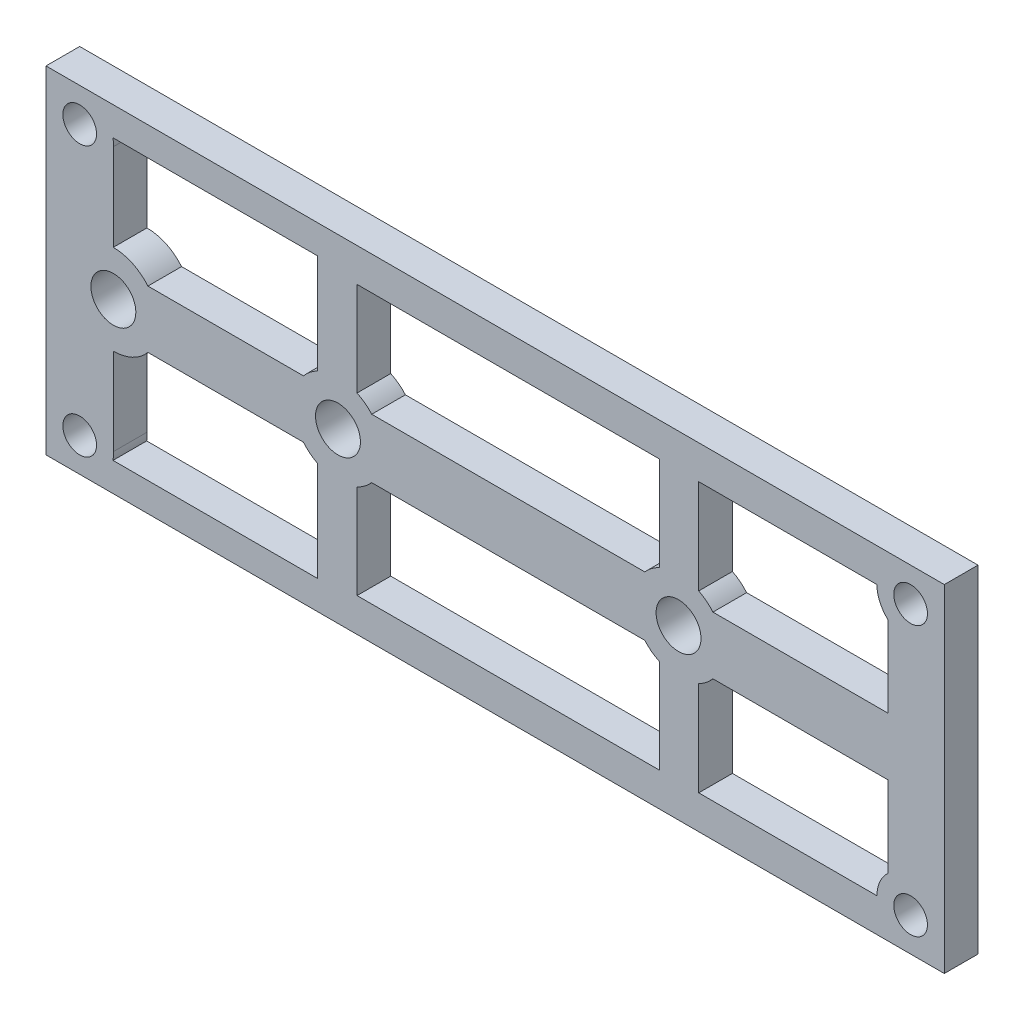
SolidWorks part; units mm, degrees
ref_plane "Front Plane" through (0, 0, 0) normal (0, 0, 1) x (1, 0, 0)
ref_plane "Top Plane" through (0, 0, 0) normal (0, 1, 0) x (1, 0, 0)
ref_plane "Right Plane" through (0, 0, 0) normal (1, 0, 0) x (0, 0, -1)
sketch "Sketch1" plane through (0, 0, 0) normal (0, 0, 1) x (1, 0, 0)
  line L1 (40, -15) -> (-40, -15)
  line L2 (40, -15) -> (40, 15)
  line L3 (40, 15) -> (-40, 15)
  line L4 (-40, -15) -> (-40, 15)
  line L5 (40, -15) -> (-40, 15) construction
  line L6 (40, 15) -> (-40, -15) construction
  point P0 (0, 0)
  dimension "D1" = 80
  dimension "D2" = 30
extrude "Boss-Extrude1" add sketch "Sketch1" along normal blind 3
sketch "Sketch2" plane through (0, 0, 3) normal (0, 0, 1) x (1, 0, 0)
  line L0 (-40, 15) -> (-40, -15) construction
  line L2 (40, 15) -> (-40, 15) construction
  line L3 (-34.0325, 12.4402) -> (-15.8, 12.4402)
  line L4 (40, -15) -> (40, 15) construction
  line L5 (-34.0097, 11.7592) -> (-34.0097, 4)
  line L6 (0, -1.65) -> (0, 1.65) construction
  line L7 (1.65, 0) -> (-1.65, 0) construction
  line L8 (-30.9254, 2.5586) -> (-17.0746, 2.5586)
  line L9 (-15.8, 12.4402) -> (-15.8, 3.5721)
  line L10 (13.3233, 2.6382) -> (-10.9933, 2.6382)
  line L11 (14.63, 3.6208) -> (14.63, 12)
  line L12 (14.63, 12) -> (-12.3, 12)
  line L13 (-12.3, 3.6208) -> (-12.3, 12)
  line L14 (35, 2.5718) -> (19.3936, 2.5718)
  line L15 (35, 2.5718) -> (35, 9.7639)
  line L16 (34, 12) -> (18.13, 12)
  line L17 (18.13, 3.5721) -> (18.13, 12)
  circle A0 centre (37, 12) radius 1.5
  circle A1 centre (-37, 12) radius 1.5
  circle A2 centre (37, -12) radius 1.5
  circle A3 centre (-37, -12) radius 1.5
  circle A4 centre (-14, 0) radius 2
  circle A5 centre (-34, 0) radius 2
  circle A6 centre (16.33, 0) radius 2
  arc A7 (-10.9933, 2.6382) -> (-12.3, 3.6208) centre (-14, 0) ccw
  arc A8 (14.63, 3.6208) -> (13.3233, 2.6382) centre (16.33, 0) ccw
  arc A9 (-30.9254, 2.5586) -> (-34.0097, 4) centre (-34, 0) ccw
  arc A10 (-34.0097, 11.7592) -> (-34.0325, 12.4402) centre (-37, 12) ccw
  arc A17 (34, 12) -> (35, 9.7639) centre (37, 12) ccw
  arc A18 (-15.8, 3.5721) -> (-17.0746, 2.5586) centre (-14, 0) ccw
  arc A19 (19.3936, 2.5718) -> (18.13, 3.5721) centre (16.33, 0) ccw
  dimension "D1" = 3
  dimension "D4" = 4
  dimension "D5" = 6
  dimension "D8" = 8
  dimension "D9" = 8
  dimension "D10" = 8
  dimension "D11" = 4
  dimension "D12" = 4
  dimension "D13" = 6
  dimension "D14" = 6
  dimension "D2" = 3
  dimension "D3" = 3
  dimension "D6" = 20
  dimension "D7" = 30.33
  dimension "D17" = 3.5
  dimension "D18" = 3.5
  dimension "D20" = 2
  dimension "D21" = 1.7
  dimension "D22" = 1.8
extrude "Cut-Extrude2" cut sketch "Sketch2" against normal through all
mirror "Mirror1" about plane through (0, 0, 0) normal (0, 1, 0) of "Cut-Extrude2"
